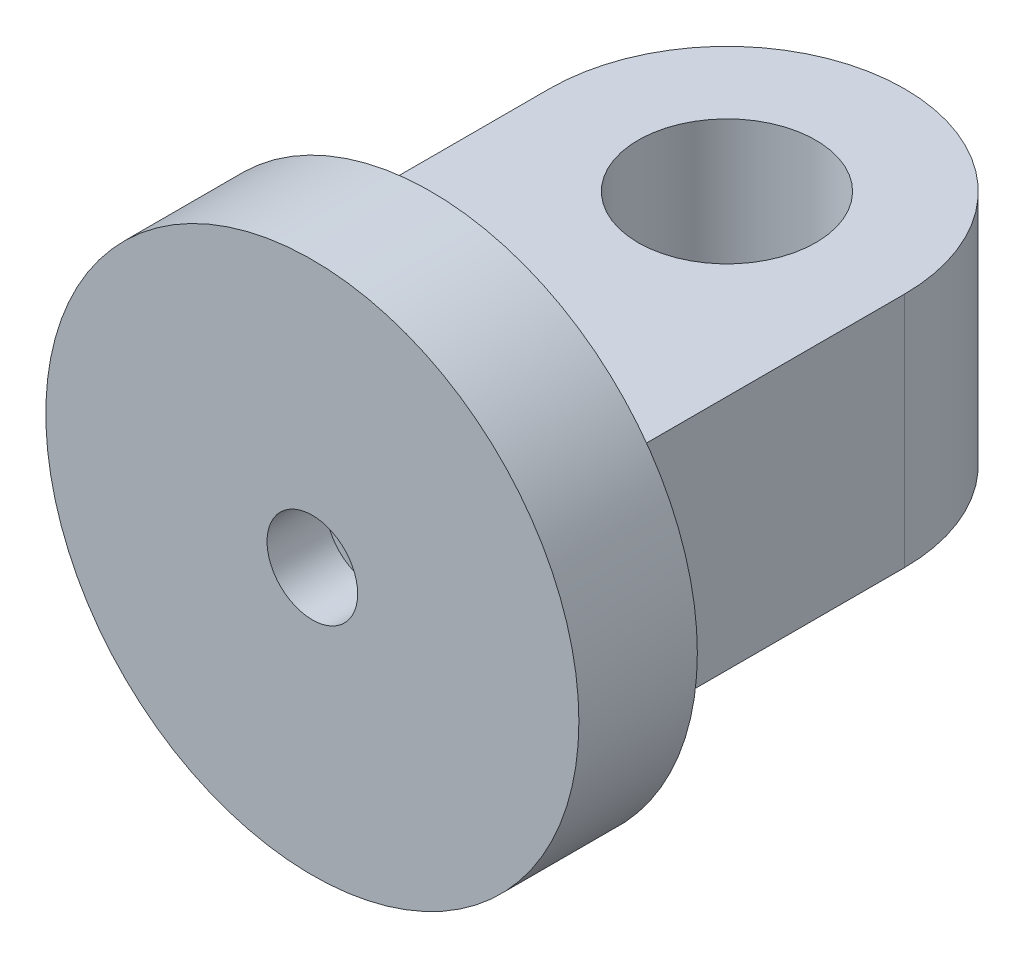
SolidWorks part; units mm, degrees
ref_plane "前视基准面" through (0, 0, 0) normal (0, 0, 1) x (1, 0, 0)
ref_plane "上视基准面" through (0, 0, 0) normal (0, 1, 0) x (1, 0, 0)
ref_plane "右视基准面" through (0, 0, 0) normal (1, 0, 0) x (0, 0, -1)
sketch "草图1" plane through (0, 0, 0) normal (0, 1, 0) x (1, 0, 0)
  line L0 (-102.3935, 0) -> (101.7335, 0) construction
  line L1 (0, 84.4691) -> (0, -80.2928) construction
  line L2 (-30, 0) -> (-30, 50)
  line L3 (-30, 0) -> (30, 0)
  line L4 (30, 0) -> (30, 50)
  arc A0 (-30, 50) -> (30, 50) centre (0, 50) cw
  circle A1 centre (0, 50) radius 15
  dimension "D1" = 30
  dimension "D2" = 30
  dimension "D3" = 50
  dimension "D4" = 30
extrude "凸台-拉伸1" add sketch "草图1" against normal mid plane 40
sketch "草图2" plane through (0, 0, 0) normal (0, 0, 1) x (1, 0, 0)
  circle A0 centre (0, 0) radius 45
  dimension "D1" = 90
extrude "凸台-拉伸2" add sketch "草图2" along normal blind 20
sketch "草图3" plane through (0, 0, 20) normal (0, 0, 1) x (1, 0, 0)
  circle A0 centre (0, 0) radius 7.65
  dimension "D1" = 15.3
extrude "切除-拉伸1" cut sketch "草图3" against normal blind 10
